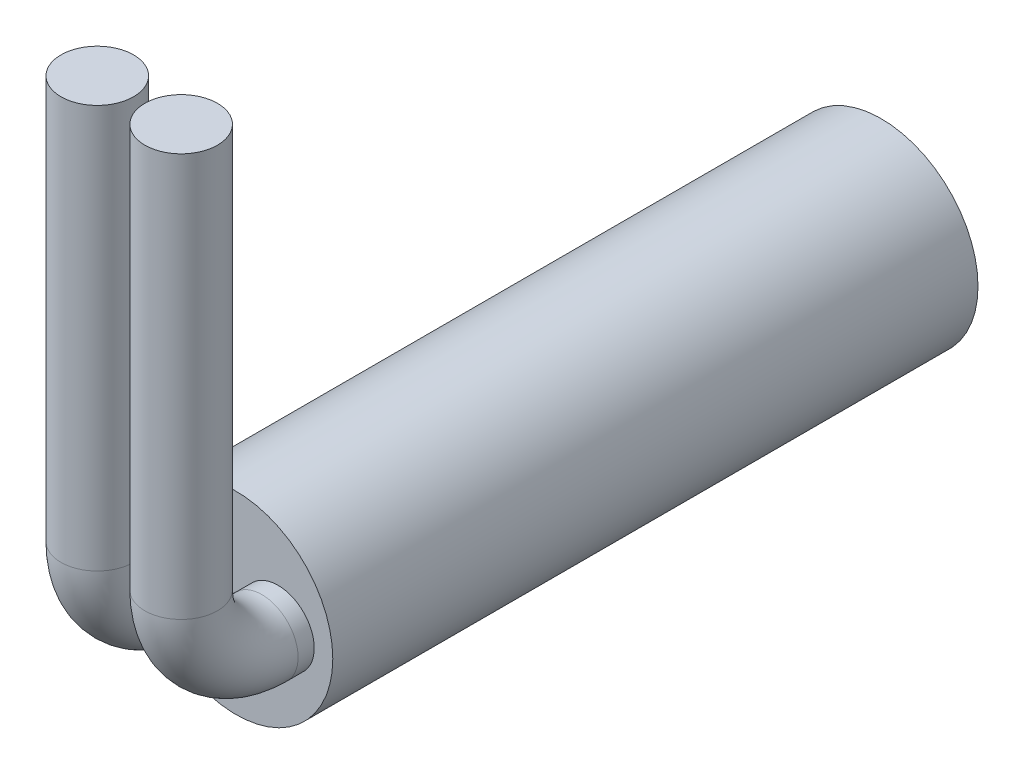
SolidWorks part; units mm, degrees
ref_plane "Front Plane" through (0, 0, 0) normal (0, 0, 1) x (1, 0, 0)
ref_plane "Top Plane" through (0, 0, 0) normal (0, 1, 0) x (1, 0, 0)
ref_plane "Right Plane" through (0, 0, 0) normal (1, 0, 0) x (0, 0, -1)
sketch "Sketch4" plane through (0, 0, 0) normal (0, 0, 1) x (1, 0, 0)
  circle A0 centre (0, 0) radius 3
extrude "Boss-Extrude1" add sketch "Sketch4" against normal blind 20 separate body
sketch "Sketch5" plane through (0, 0, 0) normal (0, 0, 1) x (1, 0, 0)
  circle A0 centre (-1.3, 0) radius 1.125
  dimension "D1" = 2.25
ref_plane "Plane2" through (-2.55, 0, 0) normal (-1, 0, 0) x (0, 0, 1)
sketch "Sketch9" plane through (-2.55, 0, 0) normal (-1, 0, 0) x (0, 0, 1)
  line L0 (3, 15) -> (3, 2.5)
  line L1 (0.5, 0) -> (0, 0)
  arc A0 (3, 2.5) -> (0.5, 0) centre (0.5, 2.5) cw
  dimension "D3" = 2.5
  dimension "D1" = 0.5
  dimension "D2" = 12.5
sweep "Sweep2" add profiles "Sketch5" path "Sketch9"
sketch "Sketch10" plane through (0, 0, 0) normal (0, 0, 1) x (1, 0, 0)
  circle A0 centre (1.3, 0) radius 1.125
  dimension "D1" = 2.25
ref_plane "Plane3" through (0.05, 0, 0) normal (-1, 0, 0) x (0, 0, 1)
sketch "Sketch15" plane through (0.05, 0, 0) normal (-1, 0, 0) x (0, 0, 1)
  line L0 (3, 15) -> (3, 2.5) construction
  line L1 (0.5, 0) -> (0, 0) construction
  line L2 (3, 15) -> (3, 2.5)
  line L3 (0.5, 0) -> (0, 0)
  arc A0 (0.5, 0) -> (3, 2.5) centre (0.5, 2.5) ccw construction
  arc A1 (0.5, 0) -> (3, 2.5) centre (0.5, 2.5) ccw
sweep "Sweep3" add profiles "Sketch10" path "Sketch15"
